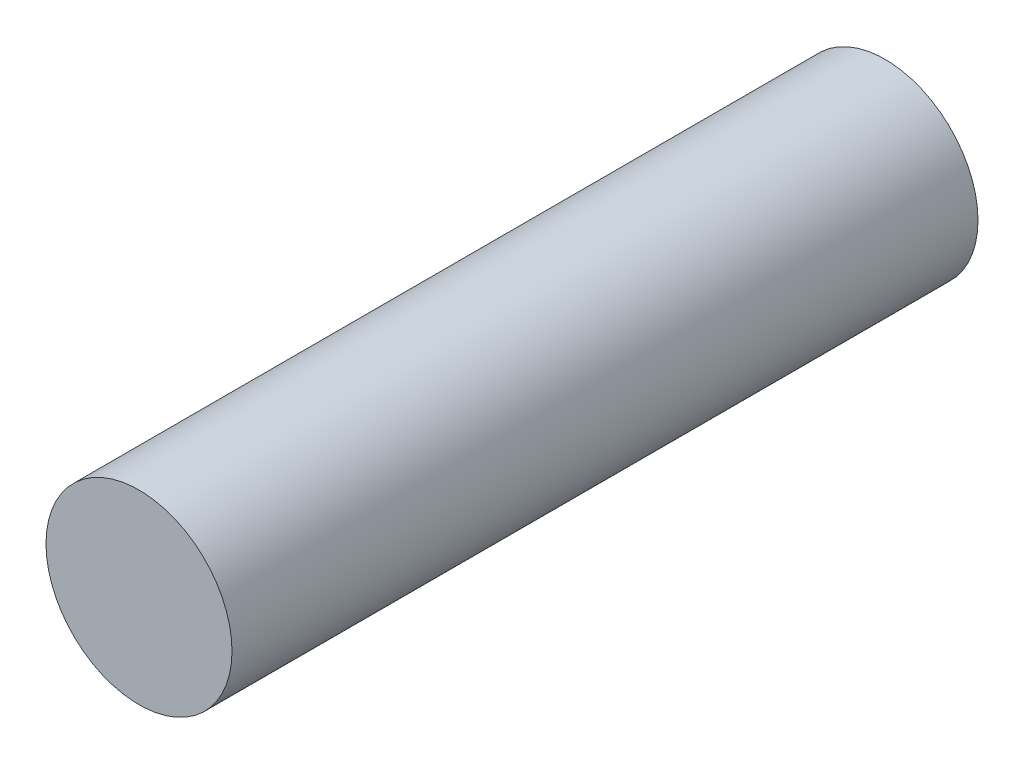
SolidWorks part; units mm, degrees
ref_plane "Front Plane" through (0, 0, 0) normal (0, 0, 1) x (1, 0, 0)
ref_plane "Top Plane" through (0, 0, 0) normal (0, 1, 0) x (1, 0, 0)
ref_plane "Right Plane" through (0, 0, 0) normal (1, 0, 0) x (0, 0, -1)
sketch "Sketch1" plane through (0, 0, 0) normal (0, 0, 1) x (1, 0, 0)
  circle A0 centre (0, 0) radius 0.935
  dimension "D1" = 1.87
extrude "Boss-Extrude1" add sketch "Sketch1" along normal blind 7.5
